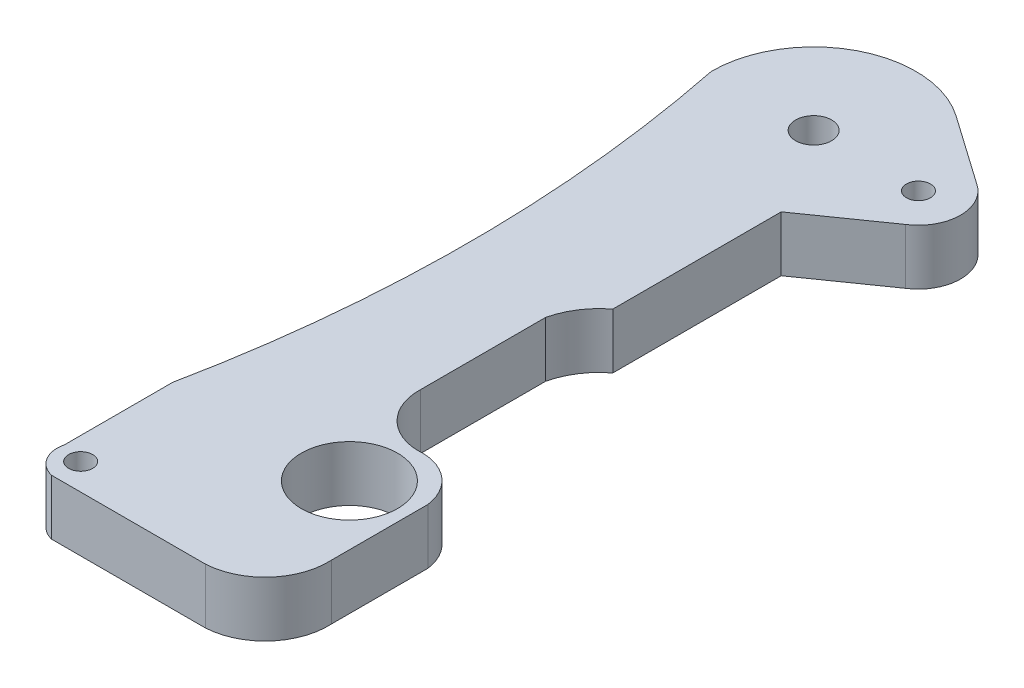
SolidWorks part; units mm, degrees
ref_plane "Front Plane" through (0, 0, 0) normal (0, 0, 1) x (1, 0, 0)
ref_plane "Top Plane" through (0, 0, 0) normal (0, 1, 0) x (1, 0, 0)
ref_plane "Right Plane" through (0, 0, 0) normal (1, 0, 0) x (0, 0, -1)
sketch "Sketch1" plane through (0, 0, 0) normal (0, 1, 0) x (1, 0, 0)
  line L0 (98.4251, 42.5572) -> (140.2114, 42.5572) construction
  line L1 (35.0753, 78.1982) -> (40.7853, 74.193)
  line L2 (40.7853, 68.2859) -> (34.7132, 64.0267)
  line L3 (34.7132, 64.0267) -> (34.7132, 50.0267)
  line L6 (23.3425, 14.7395) -> (33.8413, 14.7395)
  line L7 (41.0908, 20.2711) -> (41.0908, 28.2863)
  line L8 (32.5197, 36.2541) -> (32.5197, 46.64)
  line L9 (36.7123, 31.7391) -> (31.3478, 31.7391) construction
  line L10 (33.8413, 14.7395) -> (41.0908, 14.7395) construction
  line L11 (21.6941, 17.4633) -> (21.6941, 26.4633)
  line L12 (33.8413, 14.7395) -> (36.1322, 14.7395)
  arc A0 (35.0753, 78.1982) -> (21.6941, 71.2395) centre (30.1941, 71.2395) ccw
  circle A1 centre (30.1941, 71.2395) radius 1.5
  circle A2 centre (38.9073, 71.2395) radius 1
  arc A5 (41.0908, 28.2863) -> (36.7123, 31.7391) centre (37.1255, 27.7605) ccw
  circle A8 centre (23.5664, 16.9435) radius 1
  circle A9 centre (36.1322, 26.7162) radius 4
  arc A10 (38.6393, 70.2761) -> (38.6393, 72.2029) centre (30.1941, 71.2395) ccw
  arc A11 (40.7853, 68.2859) -> (40.7853, 74.193) centre (38.9073, 71.2395) ccw
  arc A13 (36.7123, 31.7391) -> (32.5197, 36.2541) centre (36.8735, 36.0929) cw
  arc A14 (21.6941, 17.4633) -> (23.3425, 14.7395) centre (23.8802, 16.9256) ccw
  arc A15 (21.6941, 71.2395) -> (21.6941, 26.4633) centre (-88.6742, 48.8514) cw
  arc A16 (32.5197, 46.64) -> (34.7132, 50.0267) centre (38.3165, 45.2893) cw
  arc A17 (36.1322, 14.7395) -> (41.0908, 20.2711) centre (35.8457, 19.9846) ccw
  point P7 (30.1941, 79.7395)
  point P35 (21.9542, 15.76)
  dimension "D2" = 8.5
  dimension "D3" = 3.5
  dimension "D4" = 3
  dimension "D5" = 2
  dimension "D7" = 8
  dimension "D8" = 4
  dimension "D9" = 2
  dimension "D1" = 65
  dimension "D6" = 14
  dimension "D10" = 2
  dimension "D11" = 9
extrude "Boss-Extrude1" add sketch "Sketch1" along normal blind 4.6 contours L12 A17 L7 A5 A13 L8 A16 L3 L2 A11 L1 A0 A15 L11 A14 L6 A1 A2 A8 A9
